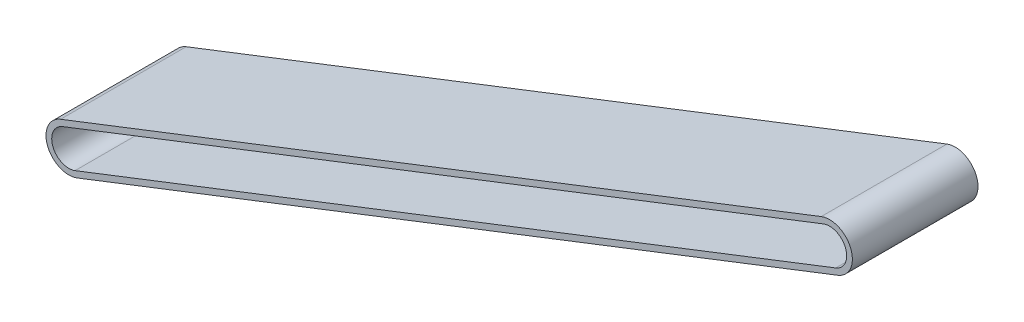
SolidWorks part; units mm, degrees
material "Rubber"
ref_plane "Front Plane" through (0, 0, 0) normal (0, 0, 1) x (1, 0, 0)
ref_plane "Top Plane" through (0, 0, 0) normal (0, 1, 0) x (1, 0, 0)
ref_plane "Right Plane" through (0, 0, 0) normal (1, 0, 0) x (0, 0, -1)
sketch "Sketch2" plane through (0, 0, 0) normal (0, 0, 1) x (1, 0, 0)
  line L0 (0, 0) -> (1, 0) construction
  line L1 (0, 0) -> (0, 1) construction
  line L2 (-18.4254, 47.3407) -> (1673.3528, 705.7961)
  line L3 (1710.2037, 611.1146) -> (18.4254, -47.3407)
  arc A0 (18.4254, -47.3407) -> (-18.4254, 47.3407) centre (0, 0) cw
  arc A1 (1673.3528, 705.7961) -> (1710.2037, 611.1146) centre (1691.7783, 658.4554) cw
extrude "Boss-Extrude1" add sketch "Sketch2" along normal mid plane 279.4
sketch "Sketch7" plane through (0, 0, 139.7) normal (0, 0, 1) x (1, 0, 0)
  line L0 (13.8191, -35.5055) -> (1705.5973, 622.9498)
  line L1 (-18.4254, 47.3407) -> (-13.8191, 35.5055) construction
  line L2 (1673.3528, 705.7961) -> (1677.9592, 693.9609) construction
  line L3 (1677.9592, 693.9609) -> (-13.8191, 35.5055)
  arc A0 (-13.8191, 35.5055) -> (13.8191, -35.5055) centre (0, 0) ccw
  arc A1 (1705.5973, 622.9498) -> (1677.9592, 693.9609) centre (1691.7783, 658.4554) ccw
  dimension "D3" = 12.7
  dimension "D1" = 12.7
  dimension "D2" = 12.7
extrude "Cut-Extrude1" cut sketch "Sketch7" against normal through all
